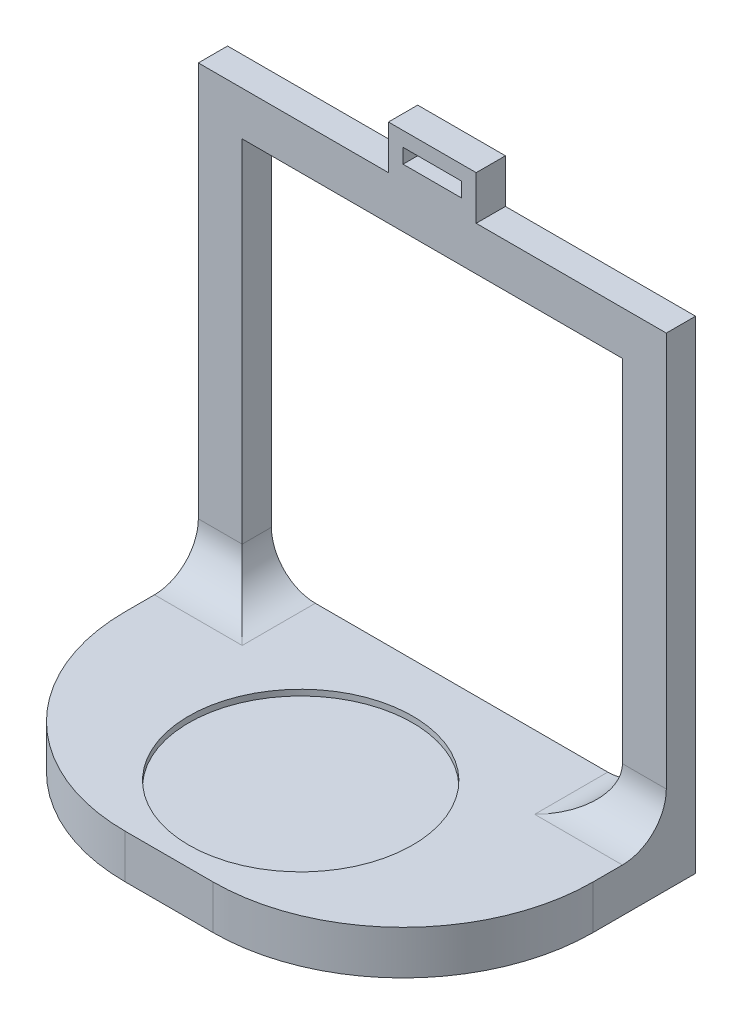
SolidWorks part; units mm, degrees
ref_plane "前视基准面" through (0, 0, 0) normal (0, 0, 1) x (1, 0, 0)
ref_plane "上视基准面" through (0, 0, 0) normal (0, 1, 0) x (1, 0, 0)
ref_plane "右视基准面" through (0, 0, 0) normal (1, 0, 0) x (0, 0, -1)
other "Configuration Table"
sketch "草图1" plane through (0, 0, 0) normal (0, 0, 1) x (1, 0, 0)
  line L0 (15, 0) -> (15, -5) construction
  line L1 (0, 0) -> (30, 0)
  line L2 (0, 0) -> (0, -15)
  line L4 (30, 0) -> (30, -15)
  line L5 (0, 0) -> (30, -15) construction
  line L6 (0, -15) -> (30, 0) construction
  line L7 (30, -15) -> (95, -15) construction
  line L8 (-65, -15) -> (0, -15) construction
  line L9 (5, -5) -> (25, -5)
  line L10 (5, -5) -> (5, -10)
  line L11 (5, -10) -> (25, -10)
  line L12 (25, -5) -> (25, -10)
  line L13 (5, -5) -> (25, -10) construction
  line L14 (5, -10) -> (25, -5) construction
  line L15 (-50, -30) -> (80, -30)
  line L16 (-65, -15) -> (0, -15)
  line L17 (-65, -15) -> (-65, -180)
  line L18 (-65, -180) -> (95, -180)
  line L19 (95, -15) -> (95, -180)
  line L20 (-65, -15) -> (95, -180) construction
  line L21 (-65, -180) -> (95, -15) construction
  line L22 (-50, -30) -> (-50, -165)
  line L23 (-50, -165) -> (80, -165)
  line L24 (80, -30) -> (80, -165)
  line L25 (-50, -30) -> (80, -165) construction
  line L26 (-50, -165) -> (80, -30) construction
  line L27 (30, -15) -> (95, -15)
  point P4 (15, -7.5)
  point P14 (15, -7.5)
  point P18 (15, -20)
  point P20 (15, -97.5)
  point P23 (15, -97.5)
  dimension "D1" = 30
  dimension "D2" = 15
  dimension "D3" = 165
  dimension "D4" = 160
  dimension "D5" = 5
  dimension "D6" = 5
  dimension "D7" = 15
  dimension "D8" = 15
  dimension "D9" = 15
  dimension "D10" = 15
  dimension "D11" = 5
extrude "凸台-拉伸1" add sketch "草图1" along normal blind 10
sketch "草图2" plane through (0, 0, 10) normal (0, 0, 1) x (1, 0, 0)
  line L0 (95, -180) -> (95, -15) construction
  line L1 (-65, -180) -> (95, -180)
  line L2 (-65, -180) -> (-65, -165)
  line L3 (-65, -165) -> (95, -165)
  line L4 (95, -180) -> (95, -165)
  line L5 (-65, -180) -> (95, -165) construction
  line L6 (-65, -165) -> (95, -180) construction
  point P4 (15, -172.5)
extrude "凸台-拉伸2" add sketch "草图2" along normal blind 90
sketch "草图3" plane through (0, -165, 0) normal (0, 1, 0) x (1, 0, 0)
  line L1 (-65, -10) -> (95, -10) construction
  line L2 (-65, -10) -> (-65, -100) construction
  line L3 (-65, -100) -> (95, -100) construction
  line L4 (95, -10) -> (95, -100) construction
  line L5 (-65, -10) -> (95, -100) construction
  line L6 (-65, -100) -> (95, -10) construction
  circle A0 centre (15, -55) radius 38.25
  point P4 (15, -55)
  dimension "D1" = 76.5
extrude "切除-拉伸1" cut sketch "草图3" against normal blind 2
fillet "圆角1" radius 15 2 edges at (87.5, -165, 10) (-57.5, -165, 10)
fillet "圆角2" radius 15 2 edges at (-50, -165, 12.5) (80, -165, 12.5)
fillet "圆角3" radius 65 2 edges at (95, -172.5, 100) (-65, -172.5, 100)
